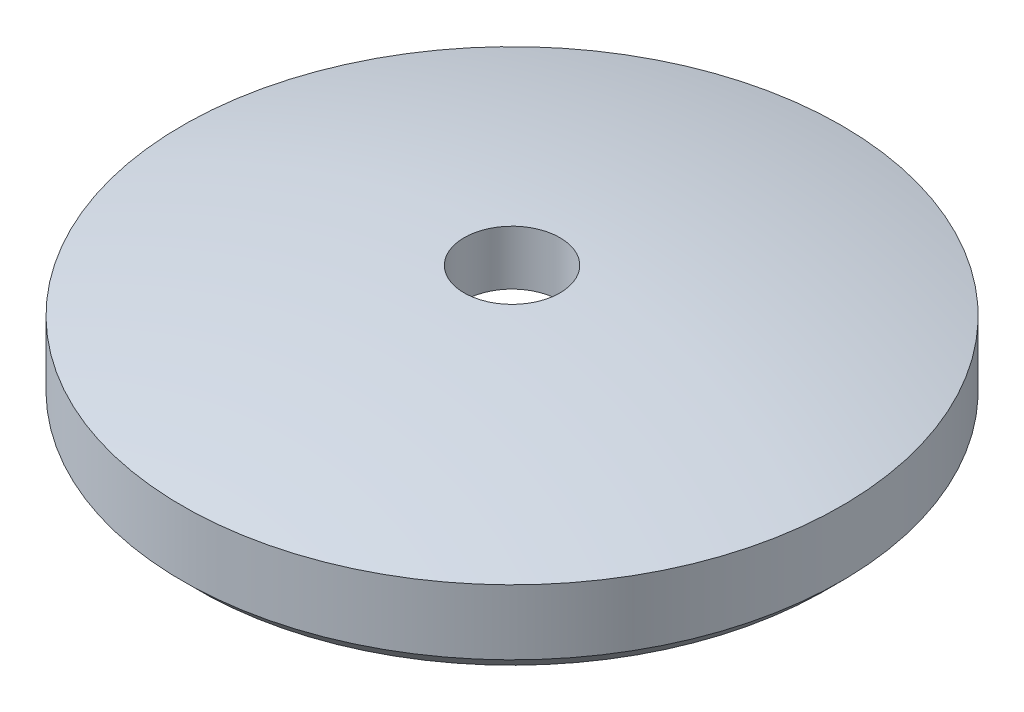
SolidWorks part; units mm, degrees
ref_plane "Alzado" through (0, 0, 0) normal (0, 0, 1) x (1, 0, 0)
ref_plane "Planta" through (0, 0, 0) normal (0, 1, 0) x (1, 0, 0)
ref_plane "Vista lateral" through (0, 0, 0) normal (1, 0, 0) x (0, 0, -1)
sketch "Sketch1" plane through (0, 0, 0) normal (0, 0, 1) x (1, 0, 0)
  line L0 (0.0747, 0.53) -> (0.0747, 0.445)
  line L1 (0.3443, 0.3354) -> (0.4892, 0.3354)
  line L2 (0.4892, 0.3354) -> (0.5142, 0.3604)
  line L3 (0.5142, 0.3604) -> (0.5142, 0.4618)
  line L4 (0, 0.53) -> (0, 0.3354) construction
  arc A0 (0.5142, 0.4618) -> (0.0747, 0.53) centre (0, -1.4023) ccw
  arc A1 (0.0747, 0.445) -> (0.3443, 0.3354) centre (0, -0.1255) cw
  dimension "D1" = 1.9338
  dimension "D2" = 0.5754
  dimension "D3" = 0.0747
  dimension "D4" = 0.3443
  dimension "D5" = 0.4892
  dimension "D6" = 0.5142
  dimension "D7" = 0.025
  dimension "D8" = 0.1264
revolve "Revolve1" add sketch "Sketch1" angle 360 about L4
